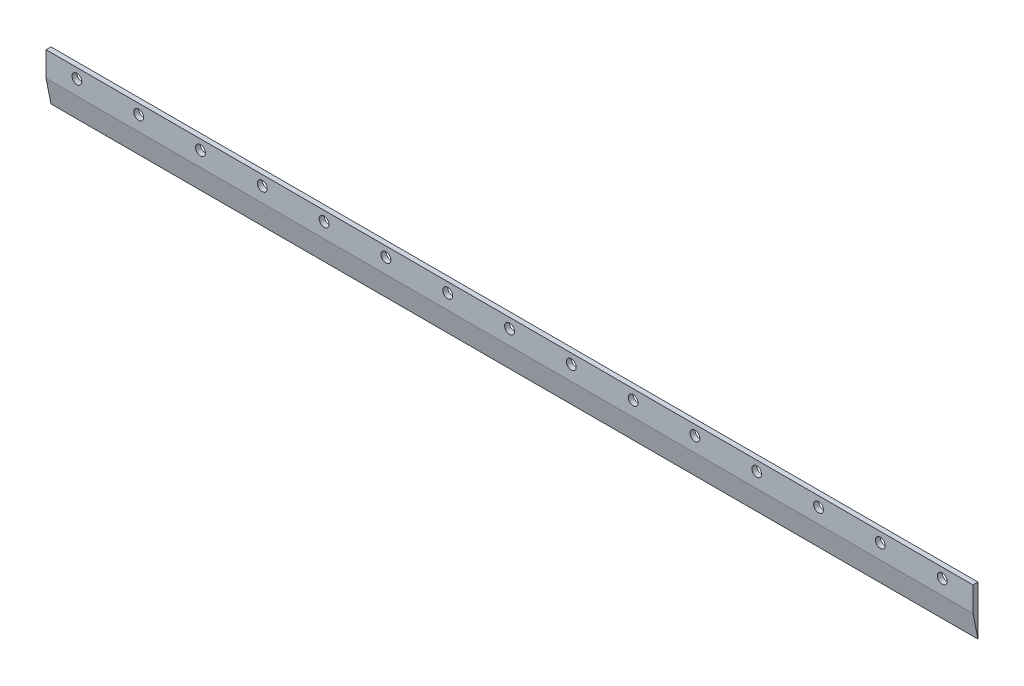
SolidWorks part; units mm, degrees
ref_plane "Alzado" through (0, 0, 0) normal (0, 0, 1) x (1, 0, 0)
ref_plane "Planta" through (0, 0, 0) normal (0, 1, 0) x (1, 0, 0)
ref_plane "Vista lateral" through (0, 0, 0) normal (1, 0, 0) x (0, 0, -1)
sketch "Croquis1" plane through (0, 0, 0) normal (0, 0, 1) x (1, 0, 0)
  line L1 (-375, -20) -> (375, -20)
  line L2 (-375, -20) -> (-375, 20)
  line L3 (-375, 20) -> (375, 20)
  line L4 (375, -20) -> (375, 20)
  line L5 (-375, -20) -> (375, 20) construction
  line L6 (-375, 20) -> (375, -20) construction
  point P0 (0, 0)
  dimension "D1" = 750
  dimension "D2" = 40
extrude "Saliente-Extruir1" add sketch "Croquis1" along normal blind 4
sketch "Croquis2" plane through (375, 0, 0) normal (1, 0, 0) x (0, 0, -1)
  line L0 (0, -20) -> (-4, 0)
  line L1 (-4, -20) -> (-4, 20) construction
  line L2 (-4, 0) -> (0, 0)
  line L3 (0, 0) -> (0, -20)
  line L8 (0, -20) -> (0, 20)
  line L9 (0, 20) -> (-4, 20)
  line L10 (-4, 20) -> (-4, -20)
  line L11 (-4, -20) -> (0, -20)
  line L12 (0, -20) -> (0, 20)
  line L13 (0, 20) -> (-4, 20)
  line L14 (-4, 20) -> (-4, -20)
  line L15 (-4, -20) -> (0, -20)
  line M7 (-4, 20) -> (-4, -20)
  line M8 (-4, -20) -> (0, -20)
  dimension "D1" = 0
extrude "Cortar-Extruir1" cut sketch "Croquis2" against normal through all contours L0 M8 M7
sketch "Croquis3" plane through (0, 0, 0) normal (0, 0, -1) x (-1, 0, 0)
  line L0 (449.2914, 0) -> (-432.142, 0) construction
  line L1 (-432.142, 12) -> (449.2914, 12) construction
  line L2 (0, 47.4243) -> (0, -46.0865) construction
  line L4 (-350, 12) -> (-300, 12) construction
  circle A0 centre (-350, 12) radius 3.9688
  circle A1 centre (-300, 12) radius 3.9688
  circle A2 centre (-250, 12) radius 3.9688
  circle A3 centre (-200, 12) radius 3.9688
  circle A4 centre (-150, 12) radius 3.9688
  circle A5 centre (-100, 12) radius 3.9688
  circle A6 centre (-50, 12) radius 3.9688
  circle A7 centre (0, 12) radius 3.9688
  circle A8 centre (50, 12) radius 3.9688
  circle A9 centre (100, 12) radius 3.9688
  circle A10 centre (150, 12) radius 3.9688
  circle A11 centre (200, 12) radius 3.9688
  circle A12 centre (250, 12) radius 3.9688
  circle A13 centre (300, 12) radius 3.9688
  circle A14 centre (350, 12) radius 3.9688
  dimension "D3" = 7.9375
  dimension "D1" = 12
  dimension "D5" = 50
  dimension "D4" = 15
extrude "Cortar-Extruir2" cut sketch "Croquis3" against normal blind 10
